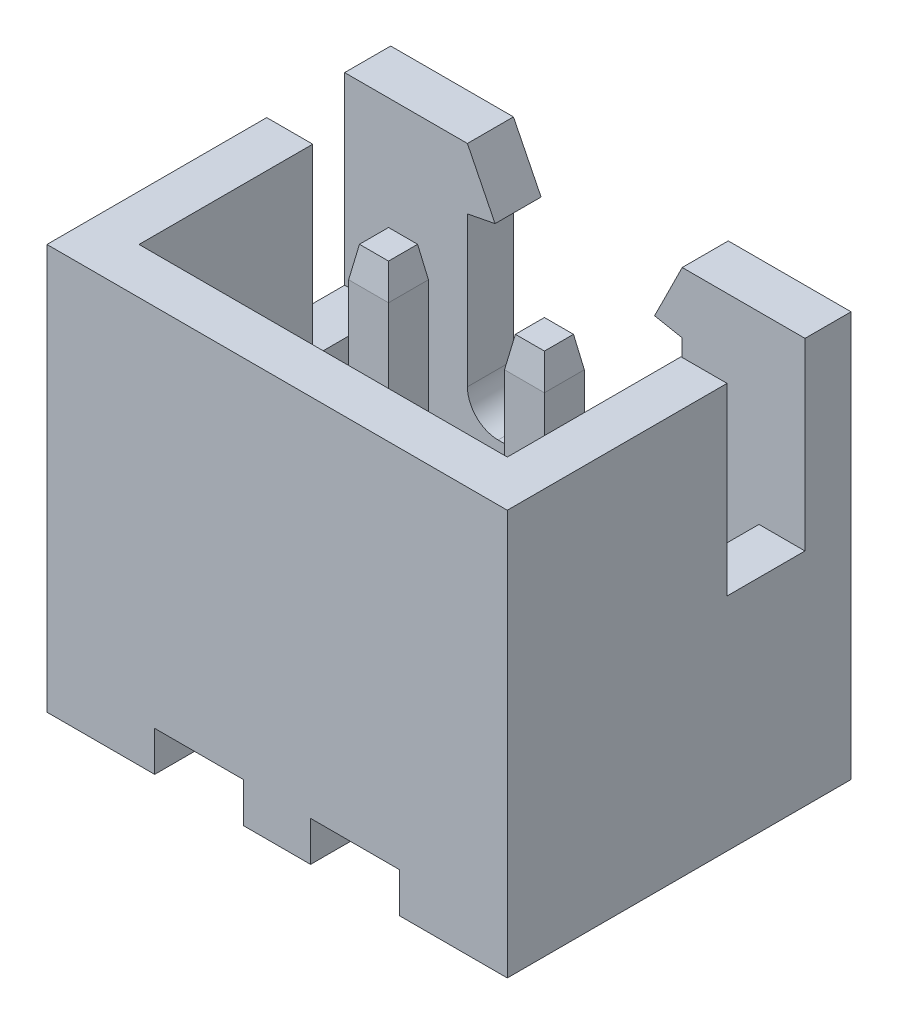
SolidWorks part; units mm, degrees
ref_plane "Front Plane" through (0, 0, 0) normal (0, 0, 1) x (1, 0, 0)
ref_plane "Top Plane" through (0, 0, 0) normal (0, 1, 0) x (1, 0, 0)
ref_plane "Right Plane" through (0, 0, 0) normal (1, 0, 0) x (0, 0, -1)
sketch "Sketch1" plane through (0, 0, 0) normal (0, 1, 0) x (1, 0, 0)
  line L1 (-3.75, 2.8) -> (3.75, 2.8)
  line L2 (-3.75, 2.8) -> (-3.75, -2.8)
  line L3 (-3.75, -2.8) -> (3.75, -2.8)
  line L4 (3.75, 2.8) -> (3.75, -2.8)
  dimension "D1" = 7.5
  dimension "D2" = 5.6
  dimension "D3" = 2.8
  dimension "D4" = 3.75
extrude "Extrude1" add sketch "Sketch1" along normal blind 6.6
sketch "Sketch2" plane through (0, 0, 2.8) normal (0, 0, 1) x (1, 0, 0)
  line L0 (-3.75, 0) -> (3.75, 0) construction
  line L1 (-1.995, 0.65) -> (-0.545, 0.65)
  line L2 (-1.995, 0.65) -> (-1.995, 0)
  line L3 (-1.995, 0) -> (-1.27, 0)
  line L4 (-0.545, 0.65) -> (-0.545, 0)
  line L5 (-1.27, 0) -> (-0.545, 0)
  line L6 (0.545, 0.65) -> (1.995, 0.65)
  line L7 (0.545, 0.65) -> (0.545, 0)
  line L8 (0.545, 0) -> (1.27, 0)
  line L9 (1.995, 0.65) -> (1.995, 0)
  line L10 (1.27, 0) -> (1.995, 0)
  dimension "D1" = 0.65
  dimension "D2" = 1.45
  dimension "D3" = 1.45
  dimension "D4" = 2.54
  dimension "D5" = 1.27
extrude "Cut-Extrude1" cut sketch "Sketch2" against normal through all
sketch "Sketch3" plane through (0, 6.6, 0) normal (0, 1, 0) x (-1, 0, 0)
  line L0 (-3.75, -2.8) -> (3.75, -2.8) construction
  line L1 (3, -2.05) -> (-3, -2.05)
  line L2 (3, -2.05) -> (3, 2.05)
  line L3 (3, 2.05) -> (-3, 2.05)
  line L4 (-3, -2.05) -> (-3, 2.05)
  line L5 (3.75, 2.8) -> (-3.75, 2.8) construction
  line L6 (-3.75, 2.8) -> (-3.75, -2.8) construction
  line L7 (3.75, -2.8) -> (3.75, 2.8) construction
  dimension "D1" = 0.75
  dimension "D2" = 0.75
  dimension "D3" = 0.75
  dimension "D4" = 0.75
extrude "Cut-Extrude2" cut sketch "Sketch3" against normal offset from surface (5.25 mm away) 0.7 up to face at (1.27, 0.65, 0)
sketch "Sketch5" plane through (-3.75, 0, 0) normal (-1, 0, 0) x (0, 0, 1)
  line L1 (-2.05, 6.6) -> (-0.78, 6.6)
  line L2 (-2.05, 6.6) -> (-2.05, 3.6)
  line L3 (-2.05, 3.6) -> (-0.78, 3.6)
  line L4 (-0.78, 6.6) -> (-0.78, 3.6)
  dimension "D1" = 3
  dimension "D2" = 1.27
extrude "Cut-Extrude3" cut sketch "Sketch5" against normal through all
sketch "Sketch6" plane through (0, 0, -2.8) normal (0, 0, -1) x (-1, 0, 0)
  line L0 (-3.75, 6.6) -> (3.75, 6.6) construction
  line L1 (-1.75, 6.6) -> (1.75, 6.6)
  line L2 (-1.75, 5.6065) -> (-1.75, 2.6665)
  line L3 (-1.75, 2.6665) -> (1.75, 2.6665)
  line L4 (1.75, 5.6065) -> (1.75, 2.6665)
  line L5 (-1.75, 6.6) -> (-1.2997, 5.6941)
  line L6 (-1.2997, 5.6941) -> (-1.75, 5.6065)
  line L7 (0, 5.3535) -> (0, 4.1856) construction
  line L8 (1.75, 6.6) -> (1.2997, 5.6941)
  line L9 (1.2997, 5.6941) -> (1.75, 5.6065)
  dimension "D1" = 3.5
  dimension "D2" = 1.75
extrude "Cut-Extrude4" cut sketch "Sketch6" against normal blind 1.2
fillet "Fillet1" radius 0.5 2 edges at (-1.75, 2.6665, -2.425) (1.75, 2.6665, -2.425)
sketch "Sketch7" plane through (0, 0, 0) normal (0, 1, 0) x (1, 0, 0)
  line L0 (-1.27, -0.0402) -> (-0.945, -0.0402)
  line L1 (-1.595, -0.0402) -> (-1.27, -0.0402)
  line L2 (-1.595, -0.0402) -> (-1.595, 0.6098)
  line L3 (-1.595, 0.6098) -> (-0.945, 0.6098)
  line L4 (-0.945, -0.0402) -> (-0.945, 0.6098)
  line L5 (0, -1.2195) -> (0, -0.5563) construction
  line L6 (1.27, -0.0402) -> (0.945, -0.0402)
  line L7 (1.595, -0.0402) -> (1.27, -0.0402)
  line L8 (1.595, -0.0402) -> (1.595, 0.6098)
  line L9 (1.595, 0.6098) -> (0.945, 0.6098)
  line L10 (0.945, -0.0402) -> (0.945, 0.6098)
  dimension "D1" = 0.65
  dimension "D2" = 0.65
  dimension "D3" = 1.27
extrude "Extrude2" add sketch "Sketch7" along normal offset from surface 0.3 and the other way blind 2 up to face at (0, 6.6, 0.8225)
chamfer "Chamfer1" distance 0.5 angle 10 16 edges at (-1.27, -2, 0.0402) (-0.945, -2, -0.2848) (-1.27, -2, -0.6098) (-1.595, -2, -0.2848) (1.595, -2, -0.2848) (1.27, -2, -0.6098) (0.945, -2, -0.2848) (1.27, -2, 0.0402) (-0.945, 6.3, -0.2848) (-1.27, 6.3, 0.0402) (-1.595, 6.3, -0.2848) (-1.27, 6.3, -0.6098) (1.27, 6.3, 0.0402) (1.595, 6.3, -0.2848) (0.945, 6.3, -0.2848) (1.27, 6.3, -0.6098)
sketch "Component_Outline" plane through (0, 0, 0) normal (0, 1, 0) x (1, 0, 0)
  line L1 (-3.75, -2.8) -> (3.75, -2.8)
  line L2 (-3.75, -2.8) -> (-3.75, 2.8)
  line L3 (-3.75, 2.8) -> (3.75, 2.8)
  line L4 (3.75, -2.8) -> (3.75, 2.8)
